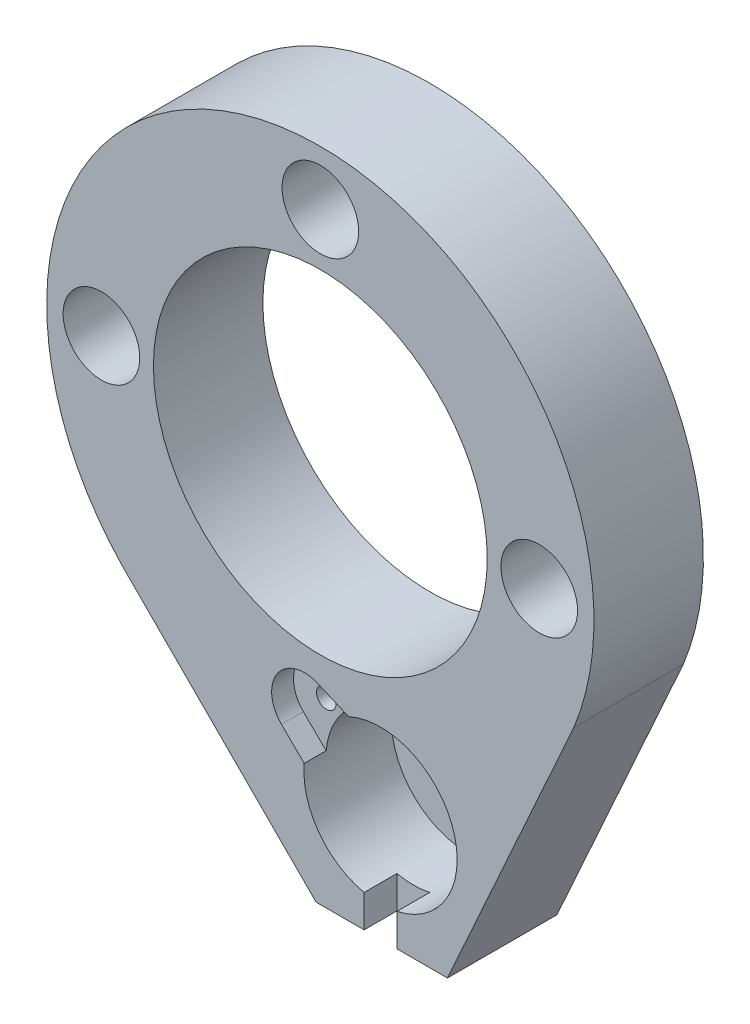
SolidWorks part; units mm, degrees
ref_plane "Front Plane" through (0, 0, 0) normal (0, 0, 1) x (1, 0, 0)
ref_plane "Top Plane" through (0, 0, 0) normal (0, 1, 0) x (1, 0, 0)
ref_plane "Right Plane" through (0, 0, 0) normal (1, 0, 0) x (0, 0, -1)
sketch "Sketch1" plane through (0, 0, 0) normal (0, 0, 1) x (1, 0, 0)
  line L0 (-0.3851, -35) -> (11.6149, -35)
  line L1 (11.6149, -35) -> (23.167, -9.3962)
  line L2 (-18.1217, -17.2222) -> (-0.3851, -35)
  arc A0 (23.167, -9.3962) -> (-18.1217, -17.2222) centre (0, 0) ccw
  circle A1 centre (0, 0) radius 15.25 construction
  dimension "D1" = 50
  dimension "D4" = 30.5
  dimension "D2" = 12
  dimension "D3" = 35
extrude "Extrude1" add sketch "Sketch1" along normal blind 10
sketch "Sketch2" plane through (0, 0, 10) normal (0, 0, 1) x (1, 0, 0)
  circle A0 centre (0, 0) radius 15.25
  dimension "D1" = 30.5
extrude "Extrude2" cut sketch "Sketch2" against normal through all
hole_wizard "Ø5.3 (5.3) Diameter Hole1" positions "3DSketch1" profile "Sketch3" hole size "Ø5.3" standard "Ansi Metric"
sketch3d "3DSketch1"
  line L0 (5.5, -25.2, 10) -> (5.5, 0, 10) construction
  line L5 (0, 0, 10) -> (15.25, 0, 10) construction
  line L6 (0, 0, 0) -> (0, 0, 10) construction
  circle A0 centre (0, 0, 10) radius 15.25 construction
  point P0 (5.5, -25.2, 10)
  point P35 (0, 0, 25.25)
  dimension "D1" = 25.2
  dimension "D2" = 5.5
sketch "Sketch3" plane through (5.5, -25.2, 10) normal (1, 0, 0) x (0, -1, 0)
  line L0 (0, 0) -> (0, 15)
  line L1 (0, 15) -> (2.65, 15)
  line L2 (2.65, 15) -> (2.65, 0)
  line L5 (2.65, 0) -> (0, 0)
  line L10 (0, 15) -> (-2.65, 15) construction
  line L11 (0, -6.35) -> (0, 107.95) construction
  dimension "Hole Dia." = 5.3
  dimension "Hole Depth" = 15
  dimension "Drill Angle" = 180
sketch "Sketch4" plane through (0, 0, 10) normal (0, 0, 1) x (1, 0, 0)
  circle A0 centre (5.5, -25.2) radius 7
  dimension "D1" = 14
extrude "Extrude3" cut sketch "Sketch4" against normal blind 8
sketch "Sketch5" plane through (0, 0, 10) normal (0, 0, 1) x (1, 0, 0)
  line L0 (-0.3851, -35) -> (11.6149, -35) construction
  line L1 (4, -35) -> (7, -35)
  line L2 (4, -35) -> (4, -32.0374)
  line L3 (4, -32.0374) -> (7, -32.0374)
  line L4 (7, -35) -> (7, -32.0374)
  circle A0 centre (5.5, -25.2) radius 7 construction
  dimension "D1" = 3
extrude "Extrude4" cut sketch "Sketch5" against normal blind 3
sketch "Sketch6" plane through (0, 0, 2) normal (0, 0, 1) x (1, 0, 0)
  line L1 (0.5, -23.691) -> (-0.5, -23.691)
  line L2 (0.5, -23.691) -> (0.5, -25.791)
  line L3 (0.5, -25.791) -> (-0.5, -25.791)
  line L4 (-0.5, -23.691) -> (-0.5, -25.791)
  circle A0 centre (5.5, -25.2) radius 2.65 construction
  dimension "D3" = 5
  dimension "D1" = 1
  dimension "D2" = 2.1
extrude "Extrude5" cut sketch "Sketch6" against normal through all
sketch "Sketch7" plane through (0, 0, 10) normal (0, 0, 1) x (1, 0, 0)
  circle A0 centre (-1.4499, -20.3708) radius 0.9
  dimension "D1" = 1.8
extrude "Extrude6" cut sketch "Sketch7" against normal blind 5
sketch "Sketch8" plane through (0, 0, 10) normal (0, 0, 1) x (1, 0, 0)
  line L0 (-3.5537, -22.5094) -> (-1.4706, -24.5587)
  line L1 (-0.2724, -17.6115) -> (2.5905, -18.8333)
  line L2 (-1.4706, -24.5587) -> (2.5905, -18.8333)
  arc A0 (-0.2724, -17.6115) -> (-3.5537, -22.5094) centre (-1.4499, -20.3708) ccw
  arc A1 (7, -32.0374) -> (4, -32.0374) centre (5.5, -25.2) ccw construction
  dimension "D1" = 6
extrude "Extrude7" cut sketch "Sketch8" against normal blind 2
sketch "Sketch9" plane through (0, 0, 0) normal (0, 0, 1) x (1, 0, 0)
  circle A0 centre (0, 0) radius 20 construction
  circle A1 centre (0, 20) radius 1.5
  circle A2 centre (-20, 0) radius 1.5
  circle A3 centre (20, 0) radius 1.5
  dimension "D1" = 40
  dimension "D2" = 3
extrude "Extrude9" cut sketch "Sketch9" along normal through all
sketch "Sketch10" plane through (0, 0, 10) normal (0, 0, 1) x (1, 0, 0)
  circle A0 centre (-20, 0) radius 3.5
  circle A1 centre (0, 20) radius 3.5
  circle A2 centre (20, 0) radius 3.5
  dimension "D1" = 7
extrude "Extrude10" cut sketch "Sketch10" against normal blind 5
